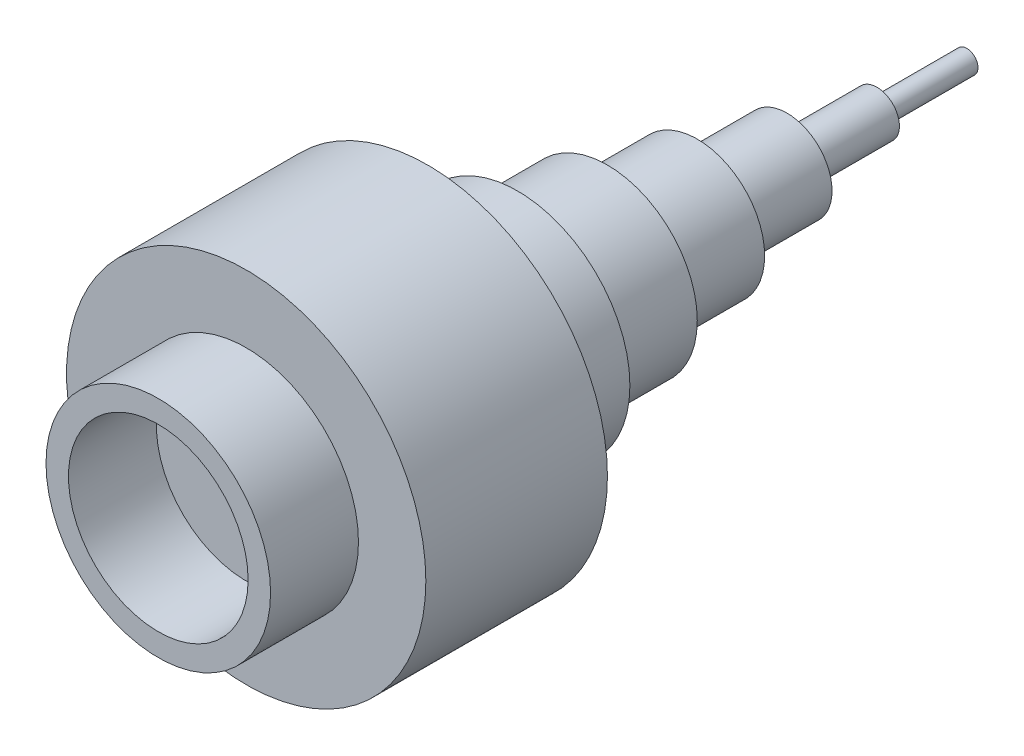
SolidWorks part; units mm, degrees
ref_plane "Front Plane" through (0, 0, 0) normal (0, 0, 1) x (1, 0, 0)
ref_plane "Top Plane" through (0, 0, 0) normal (0, 1, 0) x (1, 0, 0)
ref_plane "Right Plane" through (0, 0, 0) normal (1, 0, 0) x (0, 0, -1)
sketch "Sketch1" plane through (0, 0, 0) normal (0, 1, 0) x (1, 0, 0)
  line L0 (0, 0) -> (0, 180) construction
  line L1 (0, 180) -> (2.5, 180)
  line L2 (2.5, 180) -> (2.5, 160)
  line L3 (2.5, 160) -> (5, 160)
  line L4 (5, 160) -> (5, 140)
  line L5 (5, 140) -> (10, 140)
  line L6 (10, 140) -> (10, 120)
  line L7 (10, 120) -> (15, 120)
  line L8 (15, 120) -> (15, 100)
  line L9 (15, 100) -> (20, 100)
  line L10 (20, 100) -> (20, 80)
  line L11 (20, 80) -> (25, 80)
  line L12 (25, 80) -> (25, 60)
  line L13 (25, 60) -> (40, 60)
  line L14 (40, 60) -> (40, 19.5699)
  line L15 (40, 19.5699) -> (25, 19.5699)
  line L16 (25, 19.5699) -> (25, 0)
  line L17 (25, 0) -> (20, 0)
  line L18 (20, 0) -> (20, 19.5699)
  line L19 (20, 19.5699) -> (0, 19.5699)
  line L20 (0, 180) -> (0, 19.5699)
  dimension "D1" = 180
  dimension "D2" = 20
  dimension "D3" = 20
  dimension "D4" = 20
  dimension "D5" = 20
  dimension "D6" = 20
  dimension "D7" = 20
  dimension "D8" = 19.5699
  dimension "D9" = 40
  dimension "D10" = 50
  dimension "D11" = 80
  dimension "D12" = 50
  dimension "D13" = 40
  dimension "D14" = 30
  dimension "D15" = 20
  dimension "D16" = 10
  dimension "D17" = 5
revolve "Revolve1" add sketch "Sketch1" angle 360 about L0
